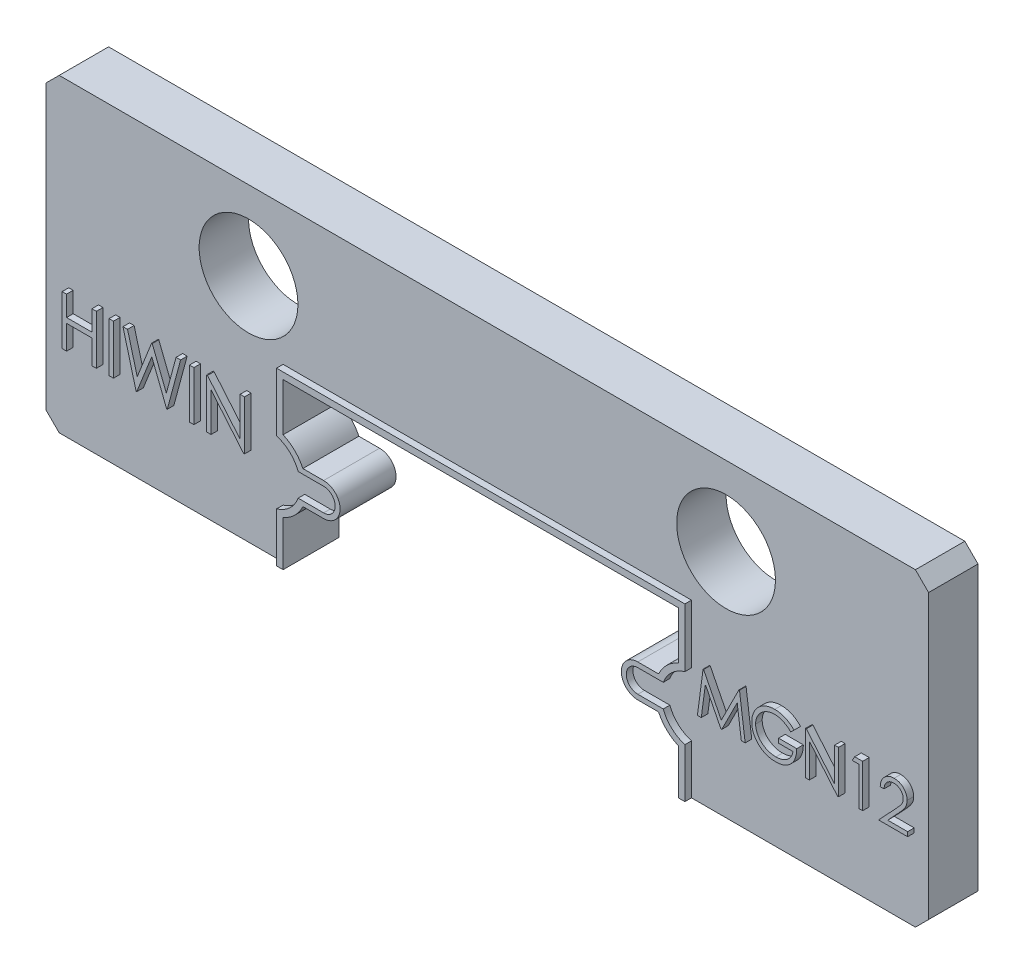
SolidWorks part; units mm, degrees
material "EPDM 60 Durometer"
ref_plane "Front Plane" through (0, 0, 0) normal (0, 0, 1) x (1, 0, 0)
ref_plane "Top Plane" through (0, 0, 0) normal (0, 1, 0) x (1, 0, 0)
ref_plane "Right Plane" through (0, 0, 0) normal (1, 0, 0) x (0, 0, -1)
sketch "Sketch1" plane through (0, 0, 0) normal (0, 0, 1) x (1, 0, 0)
  line L0 (0, 4.7) -> (0, -4.7) construction
  line L19 (-6, -4.7) -> (-13, -4.7)
  line L20 (-13, -4.7) -> (-13.4, -4.3)
  line L21 (-13.4, -4.3) -> (-13.4, 4.3)
  line L22 (-13.4, 4.3) -> (-13, 4.7)
  line L24 (-6, -4.7) -> (-6, -3.3289)
  line L25 (-6, -1.1511) -> (-6, 0.3)
  line L33 (-4.77, -2.74) -> (-5.4001, -2.74)
  line L34 (-4.77, -1.74) -> (-5.4001, -1.74)
  line L35 (-13, 4.7) -> (13, 4.7)
  line L36 (-6, 0.3) -> (6, 0.3)
  line L37 (6, -1.1511) -> (6, 0.3)
  line L38 (4.77, -1.74) -> (5.4001, -1.74)
  line L39 (4.77, -2.74) -> (5.4001, -2.74)
  line L40 (6, -4.7) -> (6, -3.3289)
  line L41 (6, -4.7) -> (13, -4.7)
  line L42 (13, -4.7) -> (13.4, -4.3)
  line L43 (13.4, -4.3) -> (13.4, 4.3)
  line L44 (13.4, 4.3) -> (13, 4.7)
  circle A6 centre (-6.48, -2.24) radius 1.19 construction
  circle A7 centre (-4.77, -2.24) radius 0.5 construction
  arc A10 (-6, -3.3289) -> (-5.4001, -2.74) centre (-6.48, -2.24) ccw
  arc A11 (-5.4001, -1.74) -> (-6, -1.1511) centre (-6.48, -2.24) ccw
  arc A12 (-4.77, -2.74) -> (-4.77, -1.74) centre (-4.77, -2.24) ccw
  arc A13 (5.4001, -1.74) -> (6, -1.1511) centre (6.48, -2.24) cw
  arc A14 (4.77, -2.74) -> (4.77, -1.74) centre (4.77, -2.24) cw
  arc A15 (6, -3.3289) -> (5.4001, -2.74) centre (6.48, -2.24) cw
  point P3 (0, 0)
  point P17 (0, 0.3)
  point P26 (0, 0.3)
  dimension "D10" = 1
  dimension "D12" = 2.54
  dimension "D8" = 9.4
  dimension "D9" = 2.38
  dimension "D11" = 2.54
  dimension "D13" = 4.77
  dimension "D14" = 6.48
  dimension "D1" = 0.4
  dimension "D2" = 0.4
  dimension "D3" = 6
  dimension "D4" = 6
  dimension "D5" = 13.4
  dimension "D6" = 0.4
  dimension "D7" = 5
extrude "Boss-Extrude1" add sketch "Sketch1" against normal blind 1.5
sketch "Sketch2" plane through (0, 0, 0) normal (0, 0, 1) x (1, 0, 0)
  line L1 (-6, -1.1511) -> (-6, 0.3) construction
  line L2 (-6, -4.7) -> (-13, -4.7) construction
  line L3 (6, -1.1511) -> (6, 0.3) construction
  line L4 (6, -4.7) -> (13, -4.7) construction
  circle A0 centre (-7.25, 2.3) radius 1.5
  circle A1 centre (7.25, 2.3) radius 1.5
  dimension "D1" = 1.25
  dimension "D2" = 7
  dimension "D3" = 1.25
  dimension "D4" = 7
extrude "Cut-Extrude1" cut sketch "Sketch2" against normal through all
sketch "Sketch3" plane through (0, 0, 0) normal (0, 0, 1) x (1, 0, 0)
  line L0 (-6.48, -2.24) -> (-13.4, -2.24) construction
  line L1 (-13.4, -4.3) -> (-13.4, 4.3) construction
  line L2 (6.48, -2.24) -> (13.4, -2.24) construction
  line L3 (13.4, -4.3) -> (13.4, 4.3) construction
  text T0 "HIWIN" font "Century Gothic" height 1.5
  text T1 "MGN12" font "Century Gothic" height 1.3
extrude "Boss-Extrude2" add sketch "Sketch3" along normal blind 0.2
sketch "Sketch4" plane through (0, 0, 0) normal (0, 0, 1) x (1, 0, 0)
  line L0 (-6.2, -4.7) -> (-6.2, -3.2)
  line L1 (-6, -4.7) -> (-13, -4.7) construction
  line L2 (-6, -4.7) -> (-6, -3.3289) construction
  line L3 (-6.2, -4.7) -> (-6, -4.7)
  line L4 (-6, -4.7) -> (-6, -3.3289)
  line L5 (-5.4001, -2.74) -> (-4.77, -2.74)
  line L6 (-4.77, -1.74) -> (-5.4001, -1.74)
  line L7 (-6, -1.1511) -> (-6, 0.3) construction
  line L8 (-6, -1.1511) -> (-6, 0.3)
  line L9 (-6.2, 0.5) -> (6.2, 0.5)
  line L10 (-6.2, 0.5) -> (-6.2, -1.28)
  line L11 (-6, 0.3) -> (6, 0.3) construction
  line L12 (6, -1.1511) -> (6, 0.3)
  line L13 (-6, 0.3) -> (6, 0.3)
  line L14 (0, 0.3) -> (0, -4.7) construction
  line L15 (-4.77, -2.59) -> (-5.5433, -2.59)
  line L16 (-4.77, -1.89) -> (-5.5433, -1.89)
  line L17 (6.2, 0.5) -> (6.2, -1.28)
  line L18 (4.77, -1.74) -> (5.4001, -1.74)
  line L19 (4.77, -1.89) -> (5.5433, -1.89)
  line L20 (4.77, -2.59) -> (5.5433, -2.59)
  line L21 (5.4001, -2.74) -> (4.77, -2.74)
  line L22 (6.2, -4.7) -> (6.2, -3.2)
  line L23 (6, -4.7) -> (6, -3.3289)
  line L24 (6.2, -4.7) -> (6, -4.7)
  circle A0 centre (-6.48, -2.24) radius 1 construction
  circle A1 centre (-4.77, -2.24) radius 0.35 construction
  arc A2 (-6, -3.3289) -> (-5.4001, -2.74) centre (-6.48, -2.24) ccw
  arc A3 (-6, -3.3289) -> (-5.4001, -2.74) centre (-6.48, -2.24) ccw construction
  arc A4 (-4.77, -2.74) -> (-4.77, -1.74) centre (-4.77, -2.24) ccw
  arc A5 (-4.77, -2.74) -> (-4.77, -1.74) centre (-4.77, -2.24) ccw construction
  arc A6 (-5.4001, -1.74) -> (-6, -1.1511) centre (-6.48, -2.24) ccw
  arc A7 (-6.2, -3.2) -> (-5.5433, -2.59) centre (-6.48, -2.24) ccw
  arc A8 (-5.5433, -1.89) -> (-6.2, -1.28) centre (-6.48, -2.24) ccw
  arc A9 (-4.77, -2.59) -> (-4.77, -1.89) centre (-4.77, -2.24) ccw
  arc A10 (5.4001, -1.74) -> (6, -1.1511) centre (6.48, -2.24) cw
  arc A11 (5.5433, -1.89) -> (6.2, -1.28) centre (6.48, -2.24) cw
  arc A12 (4.77, -2.59) -> (4.77, -1.89) centre (4.77, -2.24) cw
  arc A13 (4.77, -2.74) -> (4.77, -1.74) centre (4.77, -2.24) cw
  arc A14 (6, -3.3289) -> (5.4001, -2.74) centre (6.48, -2.24) cw
  arc A15 (6.2, -3.2) -> (5.5433, -2.59) centre (6.48, -2.24) cw
  point P33 (-5.1165, 0.5)
  point P45 (0, 0.5)
  point P48 (0, 0.5)
  point P51 (0, 0.5)
  dimension "D1" = 2
  dimension "D2" = 0.7
  dimension "D3" = 0.2
  dimension "D4" = 0.2
  dimension "D5" = 0.2
extrude "Boss-Extrude3" add sketch "Sketch4" along normal blind 0.2
